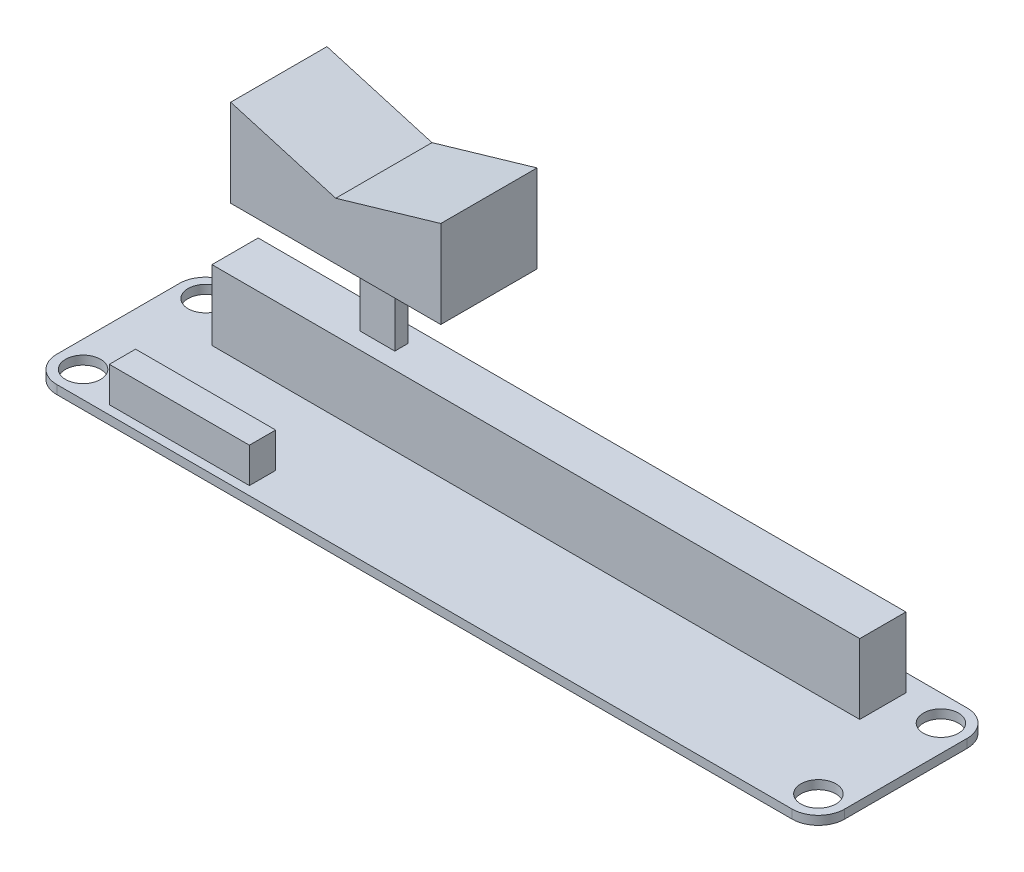
SolidWorks part; units mm, degrees
ref_plane "Front Plane" through (0, 0, 0) normal (0, 0, 1) x (1, 0, 0)
ref_plane "Top Plane" through (0, 0, 0) normal (0, 1, 0) x (1, 0, 0)
ref_plane "Right Plane" through (0, 0, 0) normal (1, 0, 0) x (0, 0, -1)
sketch "Sketch1" plane through (0, 0, 0) normal (0, 1, 0) x (1, 0, 0)
  line L1 (0, 0) -> (90, 0)
  line L2 (0, 0) -> (0, 20)
  line L3 (0, 20) -> (90, 20)
  line L4 (90, 0) -> (90, 20)
  dimension "D1" = 90
  dimension "D2" = 20
extrude "Boss-Extrude1" add sketch "Sketch1" along normal blind 1
sketch "Sketch2" plane through (0, 1, 0) normal (0, 1, 0) x (1, 0, 0)
  line L0 (90, 20) -> (0, 20) construction
  line L1 (0, 20) -> (0, 0) construction
  line L2 (45, 20) -> (45, 0) construction
  line L3 (0, 0) -> (90, 0) construction
  line L4 (0, 10) -> (90, 10) construction
  line L5 (90, 0) -> (90, 20) construction
  circle A0 centre (3, 17) radius 2
  circle A1 centre (87, 17) radius 2
  circle A2 centre (87, 3) radius 2
  circle A3 centre (3, 3) radius 2
  dimension "D1" = 4
  dimension "D2" = 3
  dimension "D3" = 3
extrude "Cut-Extrude1" cut sketch "Sketch2" against normal through all
fillet "Fillet1" radius 3 4 edges at (90, 0.5, -20) (90, 0.5, 0) (0, 0.5, 0) (0, 0.5, -20)
sketch "Sketch3" plane through (0, 1, 0) normal (0, 1, 0) x (1, 0, 0)
  line L0 (87, 20) -> (3, 20) construction
  line L1 (8, 18) -> (82, 18)
  line L2 (8, 18) -> (8, 12.7247)
  line L3 (8, 12.7247) -> (82, 12.7247)
  line L4 (82, 18) -> (82, 12.7247)
  line L5 (90, 3) -> (90, 17) construction
  line L6 (0, 17) -> (0, 3) construction
  point P8 (90, 10)
  dimension "D1" = 2
  dimension "D2" = 8
  dimension "D3" = 8
extrude "Boss-Extrude2" add sketch "Sketch3" along normal blind 8
sketch "Sketch4" plane through (0, 1, 0) normal (0, 1, 0) x (1, 0, 0)
  line L0 (0, 17) -> (0, 3) construction
  line L1 (8, 4) -> (24, 4)
  line L2 (8, 4) -> (8, 1)
  line L3 (8, 1) -> (24, 1)
  line L4 (24, 4) -> (24, 1)
  line L5 (3, 0) -> (87, 0) construction
  dimension "D1" = 16
  dimension "D2" = 3
  dimension "D3" = 8
  dimension "D4" = 1
extrude "Boss-Extrude3" add sketch "Sketch4" along normal blind 4
sketch "Sketch5" plane through (0, 9, 0) normal (0, 1, 0) x (1, 0, 0)
  line L0 (8, 18) -> (8, 12.7247) construction
  line L1 (23, 16.1123) -> (27, 16.1123)
  line L2 (23, 16.1123) -> (23, 14.6123)
  line L3 (23, 14.6123) -> (27, 14.6123)
  line L4 (27, 16.1123) -> (27, 14.6123)
  line L5 (8, 18) -> (8, 12.7247) construction
  point P6 (8, 15.3623)
  point P7 (23, 15.3623)
  dimension "D1" = 4
  dimension "D2" = 1.5
  dimension "D3" = 15
extrude "Boss-Extrude4" add sketch "Sketch5" along normal blind 10
sketch "Sketch6" plane through (0, 19, 0) normal (0, 1, 0) x (1, 0, 0)
  line L0 (27, 14.6123) -> (27, 16.1123) construction
  line L1 (13, 20.8623) -> (37, 20.8623)
  line L2 (13, 20.8623) -> (13, 9.8623)
  line L3 (13, 9.8623) -> (37, 9.8623)
  line L4 (37, 20.8623) -> (37, 9.8623)
  line L6 (27, 16.1123) -> (23, 16.1123) construction
  point P4 (27, 15.3623)
  point P7 (13, 15.3623)
  point P8 (25, 9.8623)
  point P13 (25, 16.1123)
  dimension "D1" = 24
  dimension "D2" = 11
extrude "Boss-Extrude5" add sketch "Sketch6" along normal blind 10
sketch "Sketch7" plane through (0, 0, -9.8623) normal (0, 0, 1) x (1, 0, 0)
  line L0 (37, 29) -> (25, 25.5)
  line L1 (25, 25.5) -> (13, 29)
  line L2 (13, 29) -> (37, 29)
  point P3 (25, 29)
  dimension "D1" = 3.5
extrude "Cut-Extrude2" cut sketch "Sketch7" against normal through all
